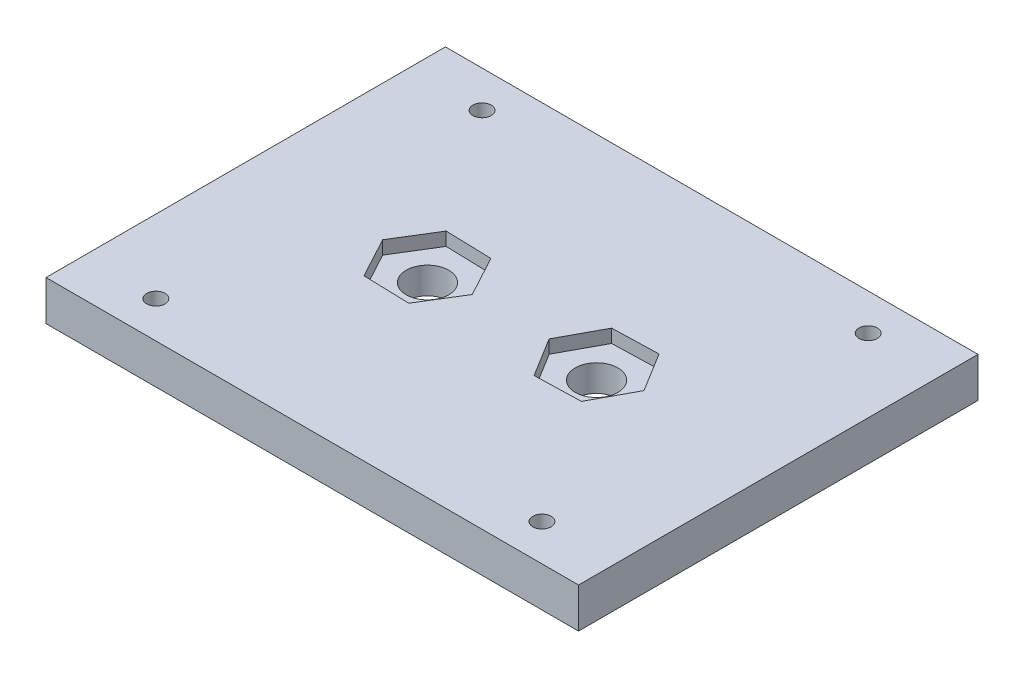
SolidWorks part; units mm, degrees
ref_plane "Front Plane" through (0, 0, 0) normal (0, 0, 1) x (1, 0, 0)
ref_plane "Top Plane" through (0, 0, 0) normal (0, 1, 0) x (1, 0, 0)
ref_plane "Right Plane" through (0, 0, 0) normal (1, 0, 0) x (0, 0, -1)
sketch "Sketch2" plane through (0, 0, 0) normal (0, 1, 0) x (1, 0, 0)
  line L1 (-40, 30) -> (40, 30)
  line L2 (-40, 30) -> (-40, -30)
  line L3 (-40, -30) -> (40, -30)
  line L4 (40, 30) -> (40, -30)
  line L5 (-40, 30) -> (40, -30) construction
  line L6 (-40, -30) -> (40, 30) construction
  point P0 (0, 0)
  dimension "D1" = 80
  dimension "D2" = 60
extrude "Boss-Extrude2" add sketch "Sketch2" along normal blind 6
sketch "Sketch3" plane through (0, 6, 0) normal (0, 1, 0) x (1, 0, 0)
  line L1 (-3.3, 0) -> (3.3, 0) construction
  line L2 (0, -3.3) -> (0, 3.3) construction
  circle A0 centre (-12.7, 0) radius 3.2
  dimension "D1" = 6.4
  dimension "D2" = 12.7
extrude "Cut-Extrude1" cut sketch "Sketch3" against normal up to next (6 mm away)
sketch "Sketch5" plane through (0, 6, 0) normal (0, 1, 0) x (1, 0, 0)
  line L1 (-9.4094, -6.0969) -> (-5.7746, -0.1987)
  line L2 (-5.7746, -0.1987) -> (-9.0653, 5.8982)
  line L3 (-9.0653, 5.8982) -> (-15.9906, 6.0969)
  line L4 (-15.9906, 6.0969) -> (-19.6254, 0.1987)
  line L5 (-19.6254, 0.1987) -> (-16.3347, -5.8982)
  line L6 (-16.3347, -5.8982) -> (-9.4094, -6.0969)
  circle A0 centre (-12.7, 0) radius 6 construction
  dimension "D1" = 12
extrude "Cut-Extrude2" cut sketch "Sketch5" against normal blind 2
mirror "Mirror2" about plane through (0, 0, 0) normal (1, 0, 0) of "Cut-Extrude1", "Cut-Extrude2"
sketch "Sketch6" plane through (0, 6, 0) normal (0, 1, 0) x (1, 0, 0)
  line L0 (0, -3.3) -> (0, 3.3) construction
  line L1 (-3.3, 0) -> (3.3, 0) construction
  circle A0 centre (-29, 24.5) radius 1.375
  dimension "D1" = 2.75
  dimension "D2" = 29
  dimension "D3" = 24.5
extrude "Cut-Extrude3" cut sketch "Sketch6" against normal up to next (6 mm away)
mirror "Mirror3" about plane through (0, 0, 0) normal (0, 0, 1) of "Cut-Extrude3"
mirror "Mirror4" about plane through (0, 0, 0) normal (1, 0, 0) of "Mirror3", "Cut-Extrude3"
